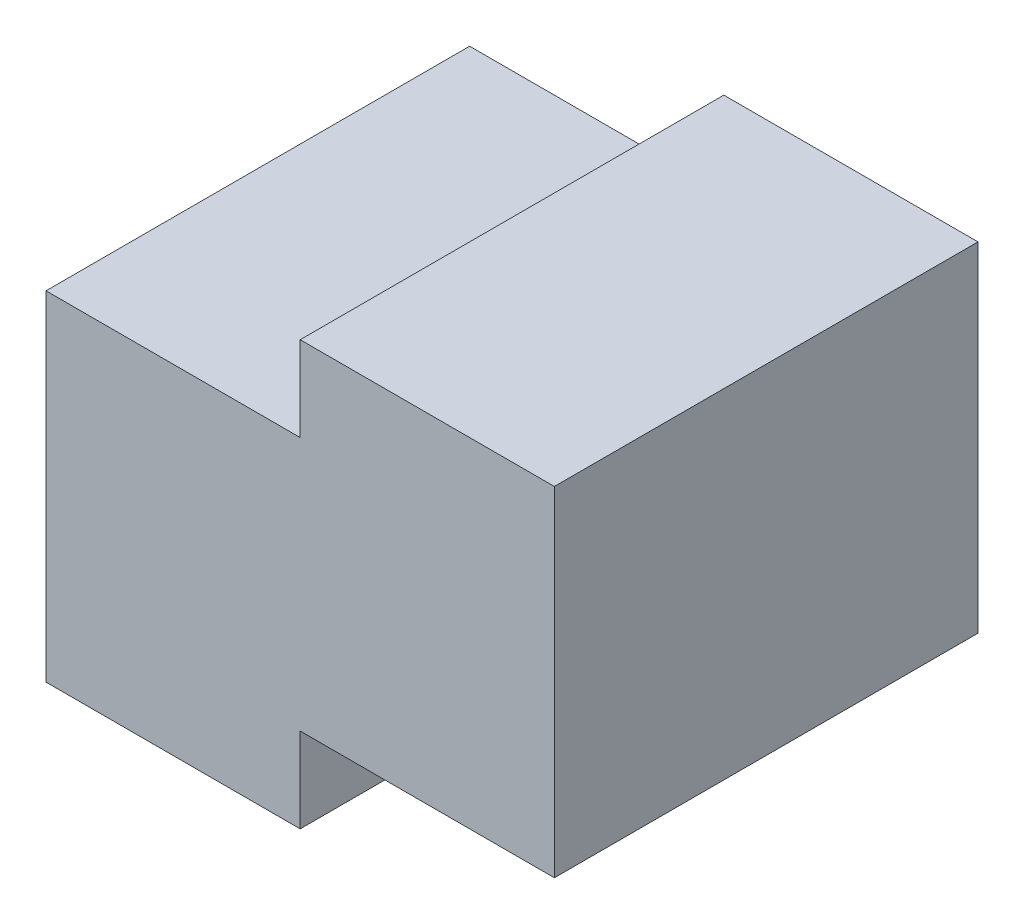
SolidWorks part; units mm, degrees
ref_plane "Front Plane" through (0, 0, 0) normal (0, 0, 1) x (1, 0, 0)
ref_plane "Top Plane" through (0, 0, 0) normal (0, 1, 0) x (1, 0, 0)
ref_plane "Right Plane" through (0, 0, 0) normal (1, 0, 0) x (0, 0, -1)
sketch "Sketch1" plane through (0, 0, 0) normal (0, 0, 1) x (1, 0, 0)
  line L0 (-30, 15) -> (-15, 15)
  line L1 (-15, 15) -> (-15, 20)
  line L2 (-15, 20) -> (0, 20)
  line L3 (0, 20) -> (0, 0)
  line L4 (0, 0) -> (-15, 0)
  line L5 (-15, 0) -> (-15, -5)
  line L6 (-15, -5) -> (-30, -5)
  line L7 (-30, -5) -> (-30, 15)
  dimension "D1" = 5
  dimension "D2" = 5
  dimension "D3" = 20
  dimension "D4" = 20
  dimension "D5" = 15
  dimension "D6" = 15
  dimension "D7" = 15
extrude "Boss-Extrude1" add sketch "Sketch1" along normal blind 25
